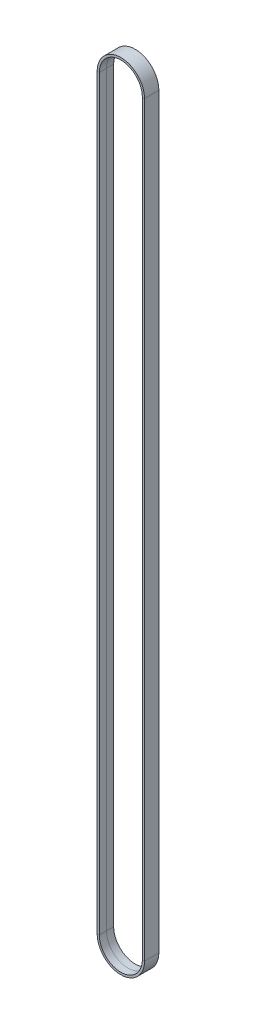
SolidWorks part; units mm, degrees
ref_plane "正面" through (0, 0, 0) normal (0, 0, 1) x (1, 0, 0)
ref_plane "平面" through (0, 0, 0) normal (0, 1, 0) x (1, 0, 0)
ref_plane "右側面" through (0, 0, 0) normal (1, 0, 0) x (0, 0, -1)
sketch "ｽｹｯﾁ2" plane through (0, 0, 0) normal (0, 0, 1) x (1, 0, 0)
  line L0 (0, 0) -> (1, 0) construction
  line L1 (0, 0) -> (0, 1) construction
  line L2 (-91.8135, 0) -> (-91.8135, 468.8942)
  line L3 (-64.8135, 468.8942) -> (-64.8135, 0)
  arc A0 (-64.8135, 0) -> (-91.8135, 0) centre (-78.3135, 0) cw
  arc A1 (-91.8135, 468.8942) -> (-64.8135, 468.8942) centre (-78.3135, 468.8942) cw
sketch3d "3Dｽｹｯﾁ4"
  line L0 (-64.8135, 468.8942, 0) -> (-64.8135, 0, 0) construction
  line L1 (-64.8135, 0, 0) -> (-64.8135, 0, -4.5)
  line L2 (-64.8135, 0, -4.5) -> (-63.4535, 0, -4.5)
  line L3 (-63.4535, 0, -4.5) -> (-63.4535, 0, 4.5)
  line L4 (-63.4535, 0, 4.5) -> (-64.8135, 0, 4.5)
  line L5 (-64.8135, 0, 4.5) -> (-64.8135, 0, 0)
  arc A1 (-64.8135, 0, 0) -> (-91.8135, 0, 0) centre (-78.3135, 0, 0) ccw construction
  point P7 (-78.3135, 0, -13.5)
  dimension "D1" = 1.36
  dimension "D2" = 1.36
  dimension "D3" = 9
  dimension "D4" = 4.5
sweep "ｽｲｰﾌﾟ1" add profiles "3Dｽｹｯﾁ4" path "ｽｹｯﾁ2"
